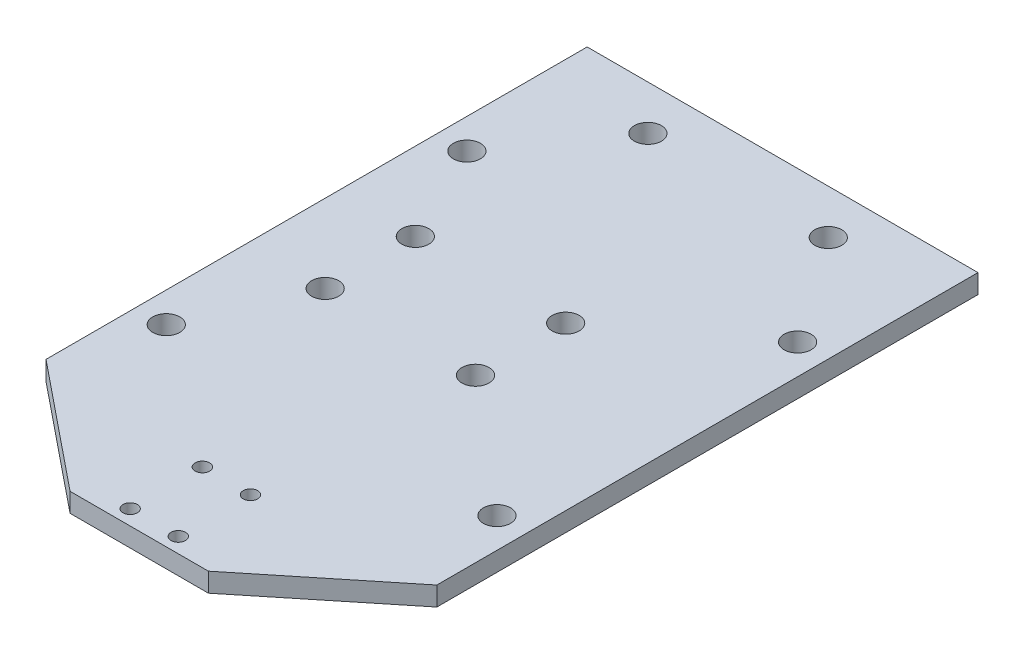
SolidWorks part; units mm, degrees
material "6061-T6 (SS)"
ref_plane "Front Plane" through (0, 0, 0) normal (0, 0, 1) x (1, 0, 0)
ref_plane "Top Plane" through (0, 0, 0) normal (0, 1, 0) x (1, 0, 0)
ref_plane "Right Plane" through (0, 0, 0) normal (1, 0, 0) x (0, 0, -1)
sketch "Sketch1" plane through (0, 0, 0) normal (0, 1, 0) x (1, 0, 0)
  line L0 (-11.5, -62) -> (-32.5, -45)
  line L1 (32.5, -45) -> (-32.5, -45)
  line L2 (32.5, -45) -> (32.5, 45)
  line L3 (32.5, 45) -> (-32.5, 45)
  line L4 (-32.5, -45) -> (-32.5, 45)
  line L5 (32.5, -45) -> (-32.5, 45) construction
  line L6 (32.5, 45) -> (-32.5, -45) construction
  line L7 (-11.5, -45) -> (11.5, -45)
  line L8 (-11.5, -45) -> (-11.5, -62)
  line L9 (-11.5, -62) -> (11.5, -62)
  line L10 (11.5, -45) -> (11.5, -62)
  line L11 (11.5, -62) -> (32.5, -45)
  line L12 (-32.5, -45) -> (32.5, -45)
  line L13 (11.5, -62) -> (-11.5, -62)
  point P0 (0, 0)
  point P10 (0, -62)
  dimension "D1" = 90
  dimension "D2" = 65
  dimension "D3" = 23
  dimension "D4" = 17
  dimension "D5" = 32.5
extrude "Boss-Extrude1" add sketch "Sketch1" along normal mid plane 3.175 contours L8 L1 L0 | L10 L11 L1 | L4 L1 L2 L3 | L10 L1 L8 L9
sketch "Sketch4" plane through (0, 1.5875, 0) normal (0, 1, 0) x (1, 0, 0)
  line L0 (-11.5, -62) -> (11.5, -62) construction
  point P0 (-4, -59.5)
  point P2 (4, -59.5)
  point P4 (4, -47.5)
  point P6 (-4, -47.5)
  point P16 (0, -62)
  dimension "D1" = 8
  dimension "D2" = 12
  dimension "D3" = 4
  dimension "D4" = 2.5
hole_wizard "M2 Clearance Hole1" positions "Sketch4" profile "Sketch3" hole size "M2" standard "ANSI Metric"
sketch "Sketch3" plane through (-4, 1.5875, 59.5) normal (1, 0, 0) x (0, 0, 1)
  line L0 (0, 0) -> (0, 3.175)
  line L1 (0, 3.175) -> (1.2, 3.175)
  line L2 (1.2, 3.175) -> (1.2, 0)
  line L5 (1.2, 0) -> (0, 0)
  line L11 (0, -6.35) -> (0, 107.95) construction
  dimension "Thru Hole Dia." = 2.4
  dimension "Thru Hole Depth" = 3.175
sketch "Sketch7" plane through (0, 1.5875, 0) normal (0, 1, 0) x (1, 0, 0)
  line L0 (-32.5, -45) -> (-32.5, 45) construction
  line L1 (32.5, -45) -> (32.5, 45) construction
  line L2 (32.5, 45) -> (-32.5, 45) construction
  point P0 (-27.5, 20)
  point P2 (27.5, 20)
  point P4 (27.5, -30)
  point P6 (-27.5, -30)
  dimension "D1" = 5
  dimension "D2" = 5
  dimension "D3" = 25
  dimension "D4" = 50
hole_wizard "M4 Clearance Hole1" positions "Sketch7" profile "Sketch6" hole size "M4" standard "ANSI Metric"
sketch "Sketch6" plane through (-27.5, 1.5875, -20) normal (1, 0, 0) x (0, 0, 1)
  line L0 (0, 0) -> (0, 3.175)
  line L1 (0, 3.175) -> (2.25, 3.175)
  line L2 (2.25, 3.175) -> (2.25, 0)
  line L5 (2.25, 0) -> (0, 0)
  line L11 (0, -6.35) -> (0, 107.95) construction
  dimension "Thru Hole Dia." = 4.5
  dimension "Thru Hole Depth" = 3.175
hole_wizard "M4 Clearance Hole2" positions "Sketch10" profile "Sketch9" hole size "M4" standard "ANSI Metric"
sketch "Sketch10" plane through (0, 1.5875, 0) normal (0, 1, 0) x (1, 0, 0)
  point P0 (-19.5, -11.575)
  point P3 (-19.5, 3.425)
  point P6 (5.5, 3.425)
  point P9 (5.5, -11.575)
sketch "Sketch9" plane through (-19.5, 1.5875, 11.575) normal (1, 0, 0) x (0, 0, 1)
  line L0 (0, 0) -> (0, 3.175)
  line L1 (0, 3.175) -> (2.25, 3.175)
  line L2 (2.25, 3.175) -> (2.25, 0)
  line L5 (2.25, 0) -> (0, 0)
  line L11 (0, -6.35) -> (0, 107.95) construction
  dimension "Thru Hole Dia." = 4.5
  dimension "Thru Hole Depth" = 3.175
hole_wizard "M4 Clearance Hole3" positions "Sketch13" profile "Sketch12" hole size "M4" standard "ANSI Metric" end condition through all
sketch "Sketch13" plane through (0, -1.5875, 0) normal (0, -1, 0) x (-1, 0, 0)
  point P0 (-15, 37.6)
  point P3 (15, 37.6)
sketch "Sketch12" plane through (15, -1.5875, -37.6) normal (1, 0, 0) x (0, 0, -1)
  line L0 (0, 0) -> (0, 3.175)
  line L1 (0, 3.175) -> (2.25, 3.175)
  line L2 (2.25, 3.175) -> (2.25, 0)
  line L5 (2.25, 0) -> (0, 0)
  line L11 (0, -6.35) -> (0, 107.95) construction
  dimension "Thru Hole Dia." = 4.5
  dimension "Thru Hole Depth" = 3.175
